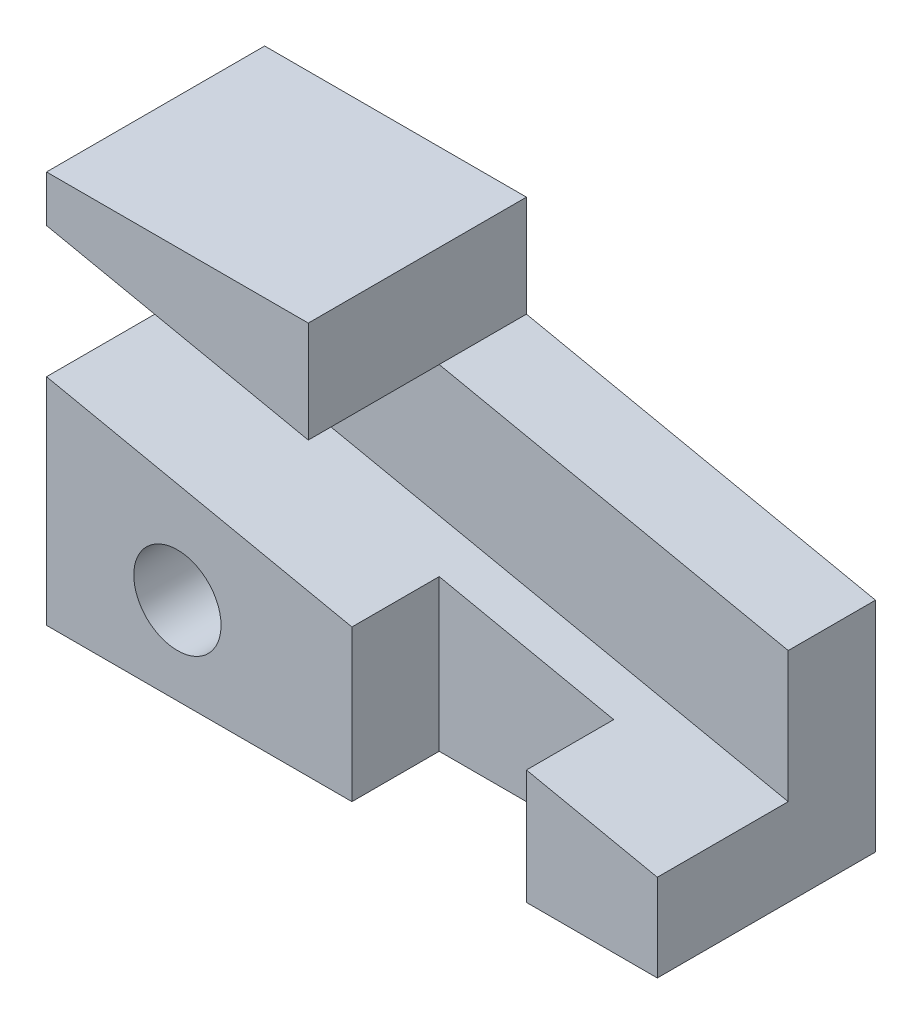
SolidWorks part; units mm, degrees
ref_plane "Front Plane" through (0, 0, 0) normal (0, 0, 1) x (1, 0, 0)
ref_plane "Top Plane" through (0, 0, 0) normal (0, 1, 0) x (1, 0, 0)
ref_plane "Right Plane" through (0, 0, 0) normal (1, 0, 0) x (0, 0, -1)
sketch "Sketch1" plane through (0, 0, 0) normal (0, 1, 0) x (1, 0, 0)
  line L1 (0, 0) -> (70, 0)
  line L2 (0, 0) -> (0, 25)
  line L3 (0, 25) -> (70, 25)
  line L4 (70, 0) -> (70, 25)
  dimension "D1" = 70
  dimension "D2" = 25
extrude "Boss-Extrude1" add sketch "Sketch1" along normal blind 45
sketch "Sketch2" plane through (0, 0, 0) normal (0, 0, 1) x (1, 0, 0)
  line L0 (0, 45) -> (0, 39.6779) construction
  line L1 (0, 45) -> (0, 0) construction
  line L2 (70, 0) -> (70, 10) construction
  line L3 (70, 45) -> (70, 0) construction
  line L4 (0, 39.6779) -> (0, 24.6779)
  line L5 (0, 24.6779) -> (70, 10)
  line L6 (70, 10) -> (70, 25)
  line L7 (70, 25) -> (0, 39.6779)
  dimension "D1" = 10
  dimension "D2" = 15
  dimension "D3" = 15
extrude "Cut-Extrude1" cut sketch "Sketch2" against normal blind 15
sketch "Sketch3" plane through (0, 0, 0) normal (0, 0, 1) x (1, 0, 0)
  line L0 (0, 45) -> (30, 45) construction
  line L1 (0, 45) -> (70, 45) construction
  line L2 (30, 45) -> (30, 33.3874)
  line L3 (70, 25) -> (0, 39.6779) construction
  line L4 (30, 33.3874) -> (70, 25)
  line L5 (70, 25) -> (70, 45)
  line L6 (70, 45) -> (30, 45)
  dimension "D1" = 30
extrude "Cut-Extrude2" cut sketch "Sketch3" against normal through all
sketch "Sketch4" plane through (0, 0, 0) normal (0, -1, 0) x (-1, 0, 0)
  line L0 (0, 0) -> (-70, 0) construction
  line L1 (-35, 0) -> (-55, 0)
  line L2 (-35, 0) -> (-35, 10)
  line L3 (-35, 10) -> (-55, 10)
  line L4 (-55, 0) -> (-55, 10)
  dimension "D1" = 10
  dimension "D2" = 20
extrude "Cut-Extrude3" cut sketch "Sketch4" against normal through all
sketch "Sketch5" plane through (0, 0, 0) normal (0, 0, 1) x (1, 0, 0)
  line L0 (0, 0) -> (15, 0) construction
  line L1 (0, 0) -> (35, 0) construction
  line L2 (15, 0) -> (15, 10) construction
  circle A0 centre (15, 10) radius 5
  dimension "D1" = 10
  dimension "D2" = 15
extrude "Cut-Extrude4" cut sketch "Sketch5" against normal through all contours A0
